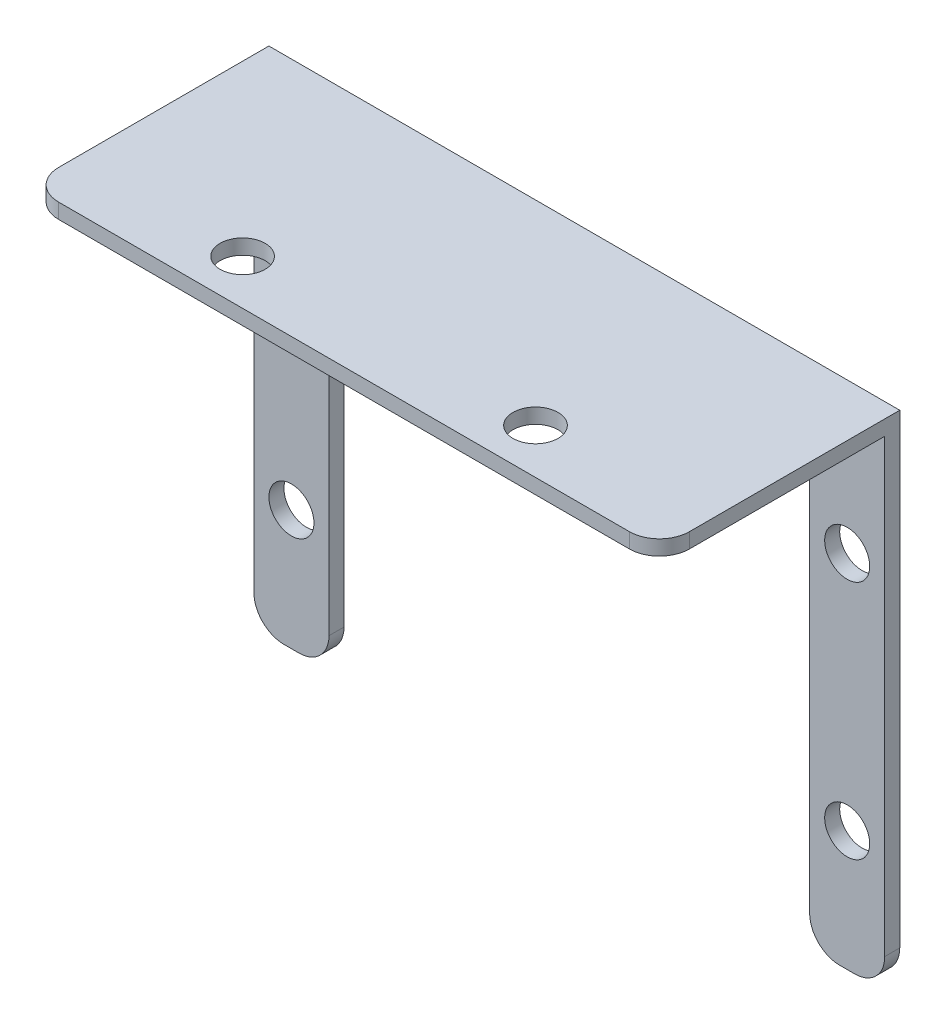
SolidWorks part; units mm, degrees
ref_plane "Front Plane" through (0, 0, 0) normal (0, 0, 1) x (1, 0, 0)
ref_plane "Top Plane" through (0, 0, 0) normal (0, 1, 0) x (1, 0, 0)
ref_plane "Right Plane" through (0, 0, 0) normal (1, 0, 0) x (0, 0, -1)
sketch "IR Holder Sketch" plane through (0, 0, 0) normal (0, 1, 0) x (1, 0, 0)
  line L0 (0, 0) -> (42, 0)
  line L2 (0, 0) -> (0, -16)
  line L3 (0, -16) -> (42, -16)
  line L4 (42, 0) -> (42, -16)
  point P0 (0, 0)
  dimension "D1" = 16
  dimension "D2" = 42
extrude "IR Holder" add sketch "IR Holder Sketch" along normal blind 1 contours L3 L4 L0 L2
sketch "Attachment Sketch" plane through (0, 0, 0) normal (0, -1, 0) x (1, 0, 0)
  line L0 (21, 0) -> (21, 16) construction
  line L1 (0, 0) -> (42, 0) construction
  line L2 (0, 16) -> (42, 16) construction
  line L3 (42, 0) -> (42, 1)
  line L4 (37, 0) -> (37, 1)
  line L5 (42, 1) -> (37, 1)
  line L6 (0, 0) -> (5, 0)
  line L7 (0, 0) -> (0, 1)
  line L8 (0, 1) -> (5, 1)
  line L9 (5, 0) -> (5, 1)
  line L10 (42, 0) -> (37, 0)
  dimension "D1" = 5
  dimension "D3" = 1
extrude "Attachment to Base" add sketch "Attachment Sketch" along normal blind 32
sketch "Attachment Holes Sketch" plane through (0, 0, 0) normal (0, 0, -1) x (-1, 0, 0)
  line L0 (-37, 0) -> (-42, 0) construction
  line L1 (-42, 1) -> (-42, -32) construction
  line L2 (-21, 1) -> (-21, 0) construction
  line L3 (-39.5, 0) -> (-39.5, -8) construction
  line L4 (-39.5, -32) -> (-39.5, -24) construction
  line L5 (-37, -32) -> (-42, -32) construction
  line L6 (0, 1) -> (-42, 1) construction
  line L7 (-5, 0) -> (-37, 0) construction
  circle A0 centre (-39.5, -8) radius 1.5
  circle A1 centre (-39.5, -24) radius 1.5
  circle A2 centre (-2.5, -24) radius 1.5
  circle A3 centre (-2.5, -8) radius 1.5
  dimension "D3" = 3
  dimension "D1" = 8
  dimension "D2" = 8
extrude "Attachment Holes" cut sketch "Attachment Holes Sketch" against normal up to next
sketch "IR Holes Sketch" plane through (0, 1, 0) normal (0, 1, 0) x (1, 0, 0)
  line L0 (21, -16) -> (21, 0) construction
  line L1 (0, -16) -> (42, -16) construction
  line L2 (0, 0) -> (42, 0) construction
  line L3 (42, -13) -> (30.75, -13) construction
  line L6 (42, 0) -> (42, -16) construction
  line L8 (0, -16) -> (42, -16) construction
  circle A2 centre (30.75, -13) radius 1.5
  circle A3 centre (11.25, -13) radius 1.5
  dimension "D3" = 3
  dimension "D4" = 3
  dimension "D1" = 11.25
extrude "IR Holes" cut sketch "IR Holes Sketch" against normal up to next
fillet "Dont cut urself" radius 2 6 edges at (5, -32, 0.5) (0, -32, 0.5) (37, -32, 0.5) (42, -32, 0.5) (42, 0.5, 16) (0, 0.5, 16)
